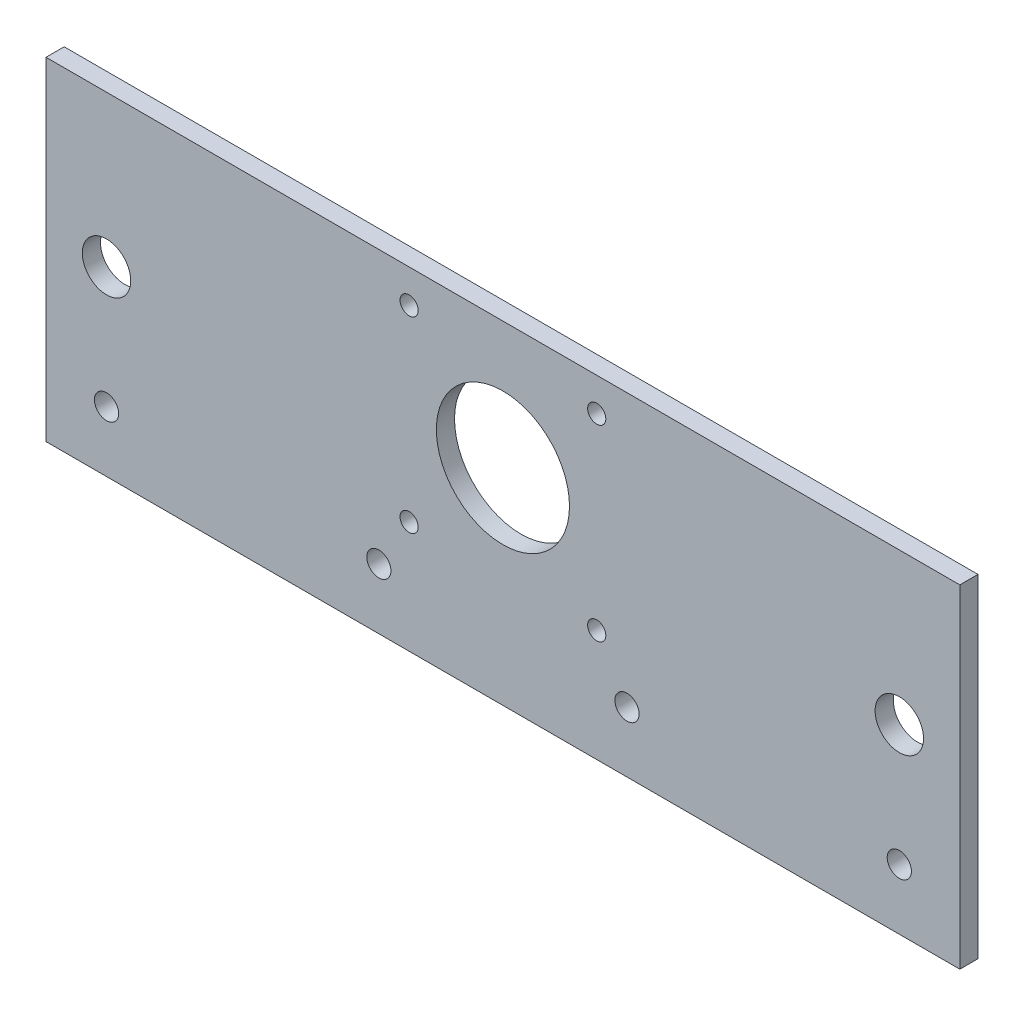
SolidWorks part; units mm, degrees
ref_plane "Ebene vorne" through (0, 0, 0) normal (0, 0, 1) x (1, 0, 0)
ref_plane "Ebene oben" through (0, 0, 0) normal (0, 1, 0) x (1, 0, 0)
ref_plane "Ebene rechts" through (0, 0, 0) normal (1, 0, 0) x (0, 0, -1)
sketch "Skizze1" plane through (0, 0, 0) normal (0, 0, 1) x (1, 0, 0)
  line L1 (0, 0) -> (151, 0)
  line L2 (0, 0) -> (0, 55)
  line L3 (0, 55) -> (151, 55)
  line L4 (151, 0) -> (151, 55)
  dimension "D1" = 55
  dimension "D2" = 151
extrude "Aufsatz-Linear austragen1" add sketch "Skizze1" along normal blind 3
sketch "Skizze2" plane through (0, 0, 3) normal (0, 0, 1) x (1, 0, 0)
  line L0 (0, 0) -> (151, 0) construction
  line L1 (0, 55) -> (0, 0) construction
  circle A0 centre (75.5, 34) radius 11
  dimension "D1" = 22
  dimension "D2" = 34
  dimension "D3" = 75.5
extrude "Schnitt-Linear austragen1" cut sketch "Skizze2" against normal blind 17
sketch "Skizze3" plane through (0, 0, 3) normal (0, 0, 1) x (1, 0, 0)
  line L0 (151, 0) -> (151, 55) construction
  line L1 (151, 55) -> (0, 55) construction
  circle A0 centre (91, 49.5) radius 1.5
  circle A1 centre (91, 18.5) radius 1.5
  circle A2 centre (60, 18.5) radius 1.5
  circle A3 centre (60, 49.5) radius 1.5
  dimension "D4" = 3
  dimension "D1" = 31
  dimension "D2" = 60
  dimension "D3" = 5.5
  dimension "D5" = 31
extrude "Schnitt-Linear austragen2" cut sketch "Skizze3" against normal blind 10
sketch "Skizze4" plane through (0, 0, 3) normal (0, 0, 1) x (1, 0, 0)
  line L0 (0, 55) -> (0, 0) construction
  line L1 (0, 0) -> (151, 0) construction
  line L2 (151, 0) -> (151, 55) construction
  circle A0 centre (141, 30) radius 4
  circle A1 centre (10, 30) radius 4
  dimension "D1" = 8
  dimension "D2" = 10
  dimension "D3" = 30
  dimension "D4" = 10
extrude "Schnitt-Linear austragen3" cut sketch "Skizze4" against normal blind 10
sketch "Skizze5" plane through (0, 0, 3) normal (0, 0, 1) x (1, 0, 0)
  line L0 (0, 0) -> (151, 0) construction
  line L1 (0, 55) -> (0, 0) construction
  line L2 (151, 0) -> (151, 55) construction
  line L3 (151, 0) -> (151, 55) construction
  circle A0 centre (10, 10) radius 2
  circle A1 centre (55, 10) radius 2
  circle A2 centre (96, 10) radius 2
  circle A3 centre (141, 10) radius 2
  dimension "D1" = 4
  dimension "D2" = 10
  dimension "D3" = 10
  dimension "D4" = 10
  dimension "D5" = 55
  dimension "D6" = 55
extrude "Schnitt-Linear austragen4" cut sketch "Skizze5" against normal blind 10
